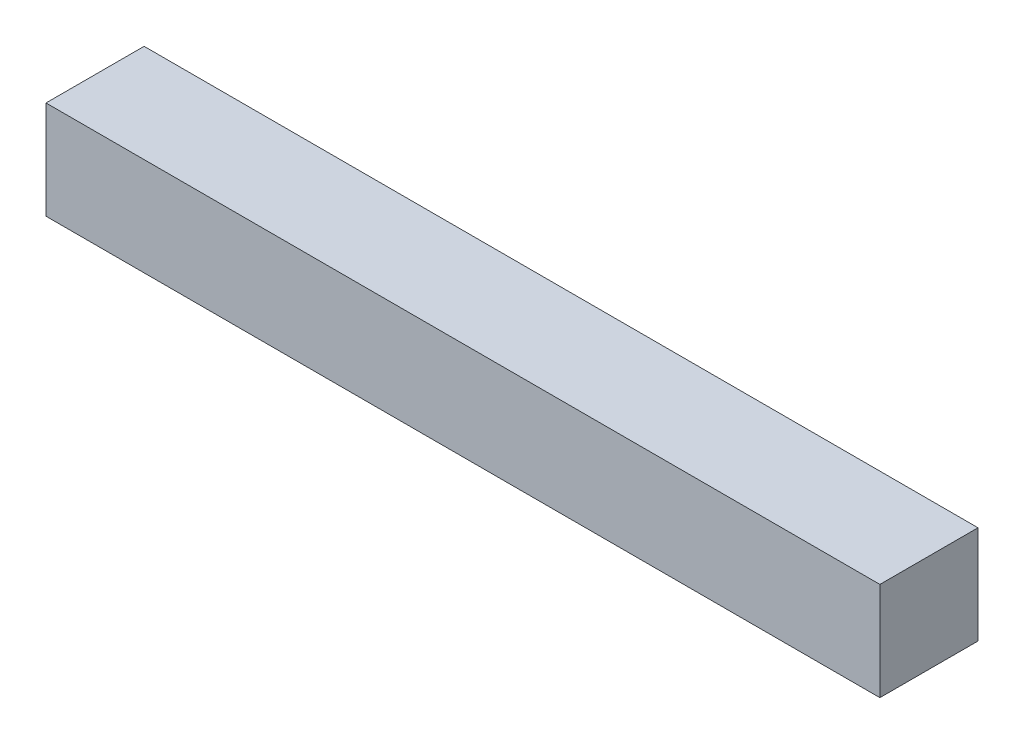
SolidWorks part; units mm, degrees
ref_plane "Спереди" through (0, 0, 0) normal (0, 0, 1) x (1, 0, 0)
ref_plane "Сверху" through (0, 0, 0) normal (0, 1, 0) x (1, 0, 0)
ref_plane "Справа" through (0, 0, 0) normal (1, 0, 0) x (0, 0, -1)
sketch "Эскиз1" plane through (0, 0, 0) normal (1, 0, 0) x (0, 0, -1)
  line L1 (-50, 50) -> (50, 50)
  line L2 (-50, 50) -> (-50, -50)
  line L3 (-50, -50) -> (50, -50)
  line L4 (50, 50) -> (50, -50)
  line L5 (-50, 50) -> (50, -50) construction
  line L6 (-50, -50) -> (50, 50) construction
  point P0 (0, 0)
extrude "Бобышка-Вытянуть1" add sketch "Эскиз1" along normal blind 850
